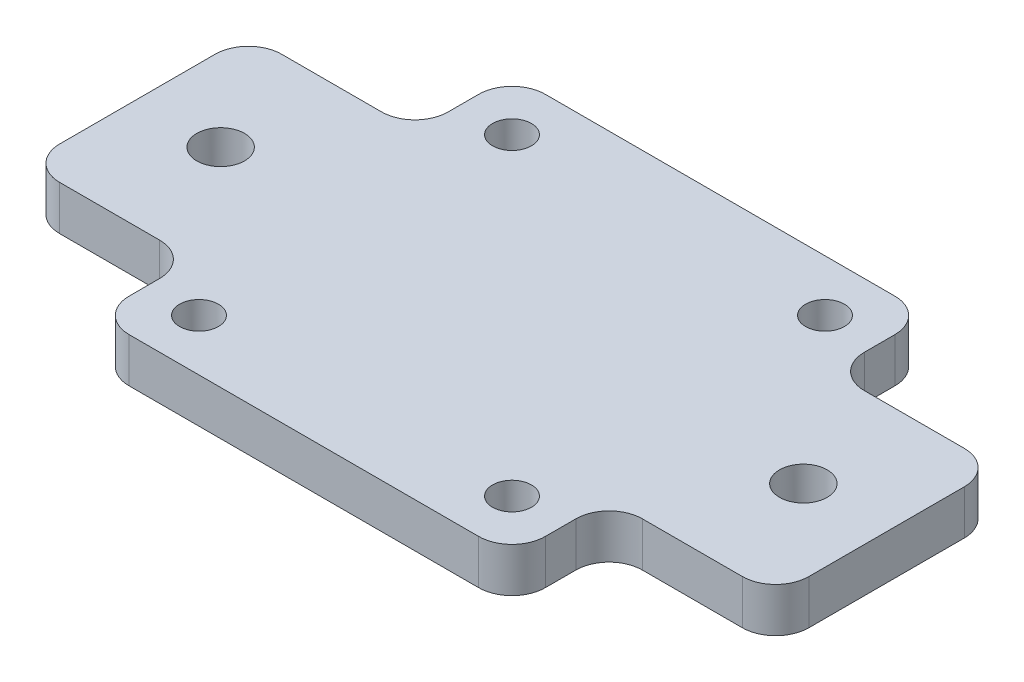
SolidWorks part; units mm, degrees
ref_plane "前视基准面" through (0, 0, 0) normal (0, 0, 1) x (1, 0, 0)
ref_plane "上视基准面" through (0, 0, 0) normal (0, 1, 0) x (1, 0, 0)
ref_plane "右视基准面" through (0, 0, 0) normal (1, 0, 0) x (0, 0, -1)
sketch "Sketch1" plane through (0, 0, 0) normal (0, 1, 0) x (1, 0, 0)
  line L1 (-18.75, -18.75) -> (18.75, -18.75)
  line L2 (-18.75, -18.75) -> (-18.75, 18.75)
  line L3 (-18.75, 18.75) -> (18.75, 18.75)
  line L4 (18.75, -18.75) -> (18.75, 18.75)
  line L5 (-18.75, -18.75) -> (18.75, 18.75) construction
  line L6 (-18.75, 18.75) -> (18.75, -18.75) construction
  point P0 (0, 0)
  dimension "D1" = 37.5
extrude "Boss-Extrude1" add sketch "Sketch1" along normal blind 4
fillet "Fillet1" radius 3 4 edges at (-18.75, 2, -18.75) (-18.75, 2, 18.75) (18.75, 2, -18.75) (18.75, 2, 18.75)
sketch "Sketch5" plane through (0, 4, 0) normal (0, 1, 0) x (1, 0, 0)
  line L1 (-14.1, -14.1) -> (14.1, -14.1) construction
  line L2 (-14.1, -14.1) -> (-14.1, 14.1) construction
  line L3 (-14.1, 14.1) -> (14.1, 14.1) construction
  line L4 (14.1, -14.1) -> (14.1, 14.1) construction
  line L5 (-14.1, -14.1) -> (14.1, 14.1) construction
  line L6 (-14.1, 14.1) -> (14.1, -14.1) construction
  circle A4 centre (-14.1, 14.1) radius 1.75
  circle A5 centre (14.1, 14.1) radius 1.75
  circle A6 centre (14.1, -14.1) radius 1.75
  circle A7 centre (-14.1, -14.1) radius 1.75
  point P0 (0, 0)
  dimension "D1" = 28.2
  dimension "D2" = 3.5
extrude "Cut-Extrude2" cut sketch "Sketch5" against normal through all both and the other way through all
sketch "Sketch6" plane through (0, 0, 0) normal (0, -1, 0) x (1, 0, 0)
  line L0 (-18.75, -15.75) -> (-18.75, 15.75) construction
  line L1 (-33.75, -10) -> (33.75, -10)
  line L2 (-33.75, -10) -> (-33.75, 10)
  line L3 (-33.75, 10) -> (33.75, 10)
  line L4 (33.75, -10) -> (33.75, 10)
  line L5 (-33.75, -10) -> (33.75, 10) construction
  line L6 (-33.75, 10) -> (33.75, -10) construction
  point P0 (0, 0)
  dimension "D1" = 20
  dimension "D2" = 15
extrude "Boss-Extrude2" add sketch "Sketch6" against normal up to surface (4 mm away) contours L2 L1 L4 L3 up to face at (-14.1, 4, 12.35)
fillet "Fillet2" radius 3 8 edges at (-33.75, 2, 10) (-18.75, 2, 10) (-18.75, 2, -10) (-33.75, 2, -10) (18.75, 2, -10) (33.75, 2, -10) (33.75, 2, 10) (18.75, 2, 10)
sketch "Sketch7" plane through (0, 4, 0) normal (0, 1, 0) x (1, 0, 0)
  line L0 (-26.25, 10) -> (-26.25, -10) construction
  line L1 (-21.75, 10) -> (-30.75, 10) construction
  line L2 (-21.75, -10) -> (-30.75, -10) construction
  line L3 (26.25, 10) -> (26.25, -10) construction
  line L4 (30.75, 10) -> (21.75, 10) construction
  line L5 (30.75, -10) -> (21.75, -10) construction
  circle A0 centre (-26.25, 0) radius 2.15
  circle A1 centre (26.25, 0) radius 2.15
  dimension "D1" = 4.3
extrude "Cut-Extrude3" cut sketch "Sketch7" against normal through all both and the other way through all
